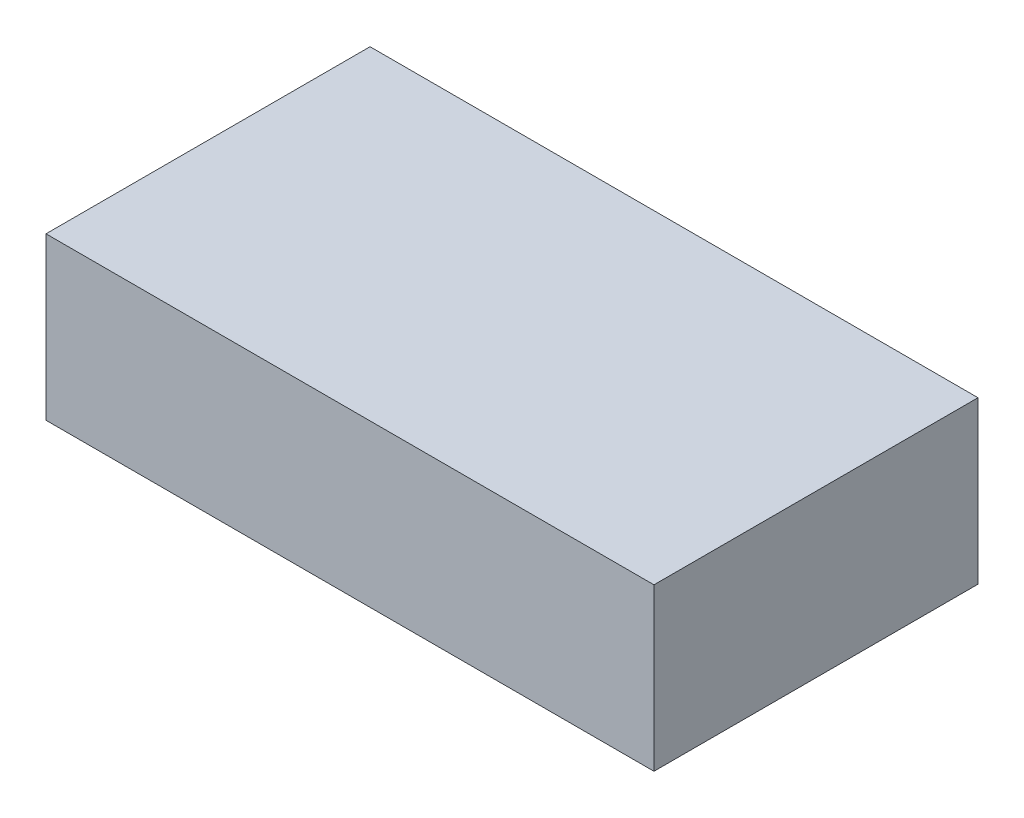
SolidWorks part; units mm, degrees
ref_plane "Alzado" through (0, 0, 0) normal (0, 0, 1) x (1, 0, 0)
ref_plane "Planta" through (0, 0, 0) normal (0, 1, 0) x (1, 0, 0)
ref_plane "Vista lateral" through (0, 0, 0) normal (1, 0, 0) x (0, 0, -1)
sketch "Croquis1" plane through (0, 0, 0) normal (0, 1, 0) x (1, 0, 0)
  line L1 (-75.057, 40.005) -> (75.057, 40.005)
  line L2 (-75.057, 40.005) -> (-75.057, -40.005)
  line L3 (-75.057, -40.005) -> (75.057, -40.005)
  line L4 (75.057, 40.005) -> (75.057, -40.005)
  line L5 (-75.057, 40.005) -> (75.057, -40.005) construction
  line L6 (-75.057, -40.005) -> (75.057, 40.005) construction
  point P0 (0, 0)
  dimension "D1" = 150.114
  dimension "D2" = 80.01
extrude "Saliente-Extruir1" add sketch "Croquis1" along normal blind 39.878
